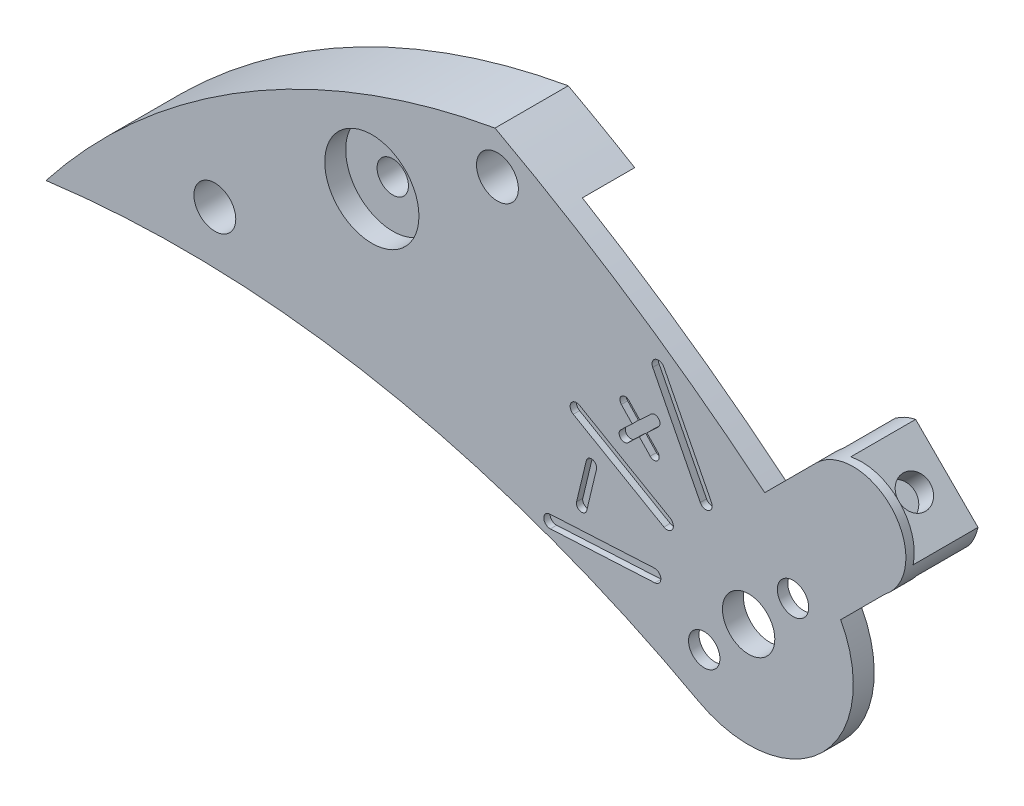
SolidWorks part; units mm, degrees
ref_plane "Alzado" through (0, 0, 0) normal (0, 0, 1) x (1, 0, 0)
ref_plane "Planta" through (0, 0, 0) normal (0, 1, 0) x (1, 0, 0)
ref_plane "Vista lateral" through (0, 0, 0) normal (1, 0, 0) x (0, 0, -1)
sketch "Croquis1" plane through (0, 0, 0) normal (0, 0, 1) x (1, 0, 0)
  line L0 (6.2596, 12.25) -> (5.199, 11.1893)
  line L1 (3.3861, 12.9119) -> (4.6235, 14.1494)
  line L2 (3, 10) -> (-3.9459, 10) construction
  line L4 (5.199, 11.1893) -> (8.6367, 11.1893) construction
  arc A0 (-3.0581, 17.2307) -> (-13.7828, 10.7835) centre (0, 0) ccw
  arc A1 (-3.5, 10) -> (-13.7828, 10.7835) centre (-10.5, -14) ccw
  arc A2 (1.7995, 7.8071) -> (5.199, 11.1893) centre (3, 10) ccw
  arc A3 (6.2596, 12.25) -> (4.6235, 14.1494) centre (5.5, 13.25) ccw
  arc A4 (3.3861, 12.9119) -> (-3.0581, 17.2307) centre (-22, -18) ccw
  arc A5 (-3.5, 10) -> (1.7995, 7.8071) centre (-10.9118, -15.4118) cw
  circle A7 centre (3, 10) radius 0.625
  circle A9 centre (-3, 16.25) radius 0.5
  circle A10 centre (-9.75, 12.25) radius 0.5
  dimension "D2" = 25
  dimension "D5" = 17.5
  dimension "D6" = 40
  dimension "D9" = 2.5
  dimension "D12" = 1.25
  dimension "D19" = 2.5
  dimension "D13" = 1.75
  dimension "D20" = 1
  dimension "D21" = 1
  dimension "D1" = 1.5
  dimension "D3" = 10.5
  dimension "D4" = 14
  dimension "D7" = 22
  dimension "D8" = 18
  dimension "D10" = 10
  dimension "D11" = 3
  dimension "D14" = 45
  dimension "D15" = 3
  dimension "D16" = 5.5
  dimension "D17" = 13.25
  dimension "D18" = 16.25
  dimension "D22" = 9.75
  dimension "D23" = 12.25
extrude "Saliente-Extruir1" add sketch "Croquis1" along normal blind 1.75
sketch "Croquis2" plane through (0, 0, 0) normal (0, 0, -1) x (-1, 0, 0)
  circle A0 centre (-3, 10) radius 7.75
  dimension "D1" = 15.5
extrude "Cortar-Extruir1" cut sketch "Croquis2" against normal blind 1.25
sketch "Croquis3" plane through (0, 0, 1.25) normal (0, 0, -1) x (-1, 0, 0)
  line L0 (-5.2726, 12.3236) -> (-4.5655, 13.0307)
  line L1 (-4.5655, 13.0307) -> (-4.919, 13.3843)
  line L2 (-4.919, 13.3843) -> (-5.6262, 12.6771)
  line L3 (-5.6262, 12.6771) -> (-5.2726, 12.3236)
  line L4 (-3.3861, 12.9119) -> (-4.6235, 14.1494) construction
  line L6 (-6.2596, 12.25) -> (-5.199, 11.1893) construction
  line L7 (-6.5086, 12.5018) -> (-4.7518, 14.2586)
  line L8 (-6.7284, 12.9891) -> (-5.2391, 14.4784)
  circle A0 centre (-3, 10) radius 0.625 construction
  arc A1 (-4.6235, 14.1494) -> (-6.2596, 12.25) centre (-5.5, 13.25) ccw construction
  arc A2 (-4.7518, 14.2586) -> (-5.2391, 14.4784) centre (-5.5, 13.25) ccw
  arc A3 (-6.7284, 12.9891) -> (-6.5086, 12.5018) centre (-5.5, 13.25) ccw
  dimension "D1" = 3.25
  dimension "D2" = 0.5
  dimension "D3" = 1
  dimension "D4" = 0.75
  dimension "D5" = 0.5
  dimension "D6" = 0.5
extrude "Saliente-Extruir2" add sketch "Croquis3" along normal blind 1.25
sketch "Croquis4" plane through (0, 0, 1.25) normal (0, 0, -1) x (-1, 0, 0)
  line L0 (-5.2391, 14.4784) -> (-6.7284, 12.9891) construction
  line L1 (-5.2391, 14.4784) -> (-6.7284, 12.9891)
  arc A0 (-5.2391, 14.4784) -> (-6.7284, 12.9891) centre (-5.5, 13.25) ccw construction
  arc A1 (-5.2391, 14.4784) -> (-6.7284, 12.9891) centre (-5.5, 13.25) ccw
extrude "Cortar-Extruir2" cut sketch "Croquis4" against normal blind 0.3
sketch "Croquis5" plane through (0, 0, 1.25) normal (0, 0, -1) x (-1, 0, 0)
  line L0 (-4.0607, 11.0607) -> (-1.9393, 8.9393) construction
  line L1 (-5.2726, 12.3236) -> (-4.5655, 13.0307) construction
  circle A0 centre (-4.0607, 11.0607) radius 0.75
  circle A1 centre (-1.9393, 8.9393) radius 0.75
  point P6 (-3, 10)
  point P7 (-3, 10)
  dimension "D2" = 1.5
  dimension "D3" = 1.5
  dimension "D1" = 3
extrude "Cortar-Extruir3" cut sketch "Croquis5" against normal blind 0.25
sketch "Croquis6" plane through (9.1517, 9.1517, 0) normal (0.7071, 0.7071, 0) x (0, 0, -1)
  line L0 (0, 5.9858) -> (-1.25, 5.9858) construction
  line L1 (0, 5.9858) -> (0, 4.9858) construction
  circle A0 centre (-0.625, 5.4858) radius 0.25 construction
  point P4 (-0.625, 5.9858)
  point P7 (0, 5.4858)
  dimension "D1" = 0.5
sketch "Croquis7" plane through (0, 0, 1.75) normal (0, 0, 1) x (1, 0, 0)
  circle A0 centre (-6, 14.5) radius 1.125
  dimension "D1" = 2.25
  dimension "D2" = 6
  dimension "D3" = 14.5
extrude "Cortar-Extruir4" cut sketch "Croquis7" against normal blind 0.5
ref_plane "Plano1" through (0, 0, 0.625) normal (0, 0, -1) x (-1, 0, 0)
sketch "Croquis8" plane through (0, 0, 1.75) normal (0, 0, 1) x (1, 0, 0)
  line L0 (0.8435, 14.2323) -> (1.9785, 12.0048) construction
  line L1 (0.9772, 14.3004) -> (2.1122, 12.0729)
  line L2 (0.7099, 14.1642) -> (1.8449, 11.9367)
  line L3 (0.7531, 9.8822) -> (-1.7435, 9.7514) construction
  line L4 (0.7609, 9.7324) -> (-1.7356, 9.6016)
  line L5 (0.7452, 10.032) -> (-1.7513, 9.9012)
  line L6 (1.9785, 12.0048) -> (3, 10) construction
  line L7 (0.7531, 9.8822) -> (3, 10) construction
  line L8 (3, 10) -> (-1.7983, 10) construction
  line L9 (3, 10) -> (-2.6707, 13.274) construction
  line L10 (-1.1136, 12.375) -> (1.0514, 11.125) construction
  line L11 (-1.0386, 12.5049) -> (1.1264, 11.2549)
  line L12 (-1.1886, 12.2451) -> (0.9764, 10.9951)
  line L13 (-0.7552, 11.4158) -> (-0.9887, 10.4434) construction
  line L14 (-0.6337, 11.3866) -> (-0.8671, 10.4142)
  line L15 (-0.8768, 11.4449) -> (-1.1102, 10.4726)
  line L16 (0.0322, 12.401) -> (0.7576, 13.0894) construction
  line L17 (-0.0538, 12.4917) -> (0.2182, 12.7498)
  line L18 (0.1183, 12.3104) -> (0.3903, 12.5685)
  line L19 (0.0507, 13.1079) -> (0.7391, 12.3825) construction
  line L20 (0.1414, 13.1939) -> (0.3995, 12.9219)
  line L21 (-0.0399, 13.0218) -> (0.2182, 12.7498)
  line L22 (3, 10) -> (-1.9711, 11.1935) construction
  line L23 (3, 10) -> (-0.4688, 13.6553) construction
  line L24 (0.3995, 12.9219) -> (0.6715, 13.1801)
  line L25 (0.5716, 12.7406) -> (0.8297, 12.4686)
  line L26 (0.3903, 12.5685) -> (0.6484, 12.2965)
  line L27 (0.5716, 12.7406) -> (0.8436, 12.9987)
  arc A0 (0.9772, 14.3004) -> (0.7099, 14.1642) centre (0.8435, 14.2323) ccw
  arc A1 (1.8449, 11.9367) -> (2.1122, 12.0729) centre (1.9785, 12.0048) ccw
  arc A2 (0.7609, 9.7324) -> (0.7452, 10.032) centre (0.7531, 9.8822) ccw
  arc A3 (-1.7513, 9.9012) -> (-1.7356, 9.6016) centre (-1.7435, 9.7514) ccw
  arc A4 (-1.0386, 12.5049) -> (-1.1886, 12.2451) centre (-1.1136, 12.375) ccw
  arc A5 (0.9764, 10.9951) -> (1.1264, 11.2549) centre (1.0514, 11.125) ccw
  arc A6 (-0.6337, 11.3866) -> (-0.8768, 11.4449) centre (-0.7552, 11.4158) ccw
  arc A7 (-1.1102, 10.4726) -> (-0.8671, 10.4142) centre (-0.9887, 10.4434) ccw
  arc A8 (-0.0538, 12.4917) -> (0.1183, 12.3104) centre (0.0322, 12.401) ccw
  arc A9 (0.8436, 12.9987) -> (0.6715, 13.1801) centre (0.7576, 13.0894) ccw
  arc A10 (0.1414, 13.1939) -> (-0.0399, 13.0218) centre (0.0507, 13.1079) ccw
  arc A11 (0.6484, 12.2965) -> (0.8297, 12.4686) centre (0.7391, 12.3825) ccw
  point P2 (1.411, 13.1185)
  point P9 (-0.4952, 9.8168)
  point P22 (-0.0311, 11.75)
  point P29 (-0.872, 10.9296)
  point P36 (0.3949, 12.7452)
  point P43 (0.3949, 12.7452)
  dimension "D1" = 30
  dimension "D2" = 2.25
  dimension "D3" = 2.25
  dimension "D4" = 33
  dimension "D5" = 33
  dimension "D6" = 2.25
  dimension "D7" = 2.5
  dimension "D8" = 2.5
  dimension "D9" = 2.5
  dimension "D10" = 0.3
  dimension "D11" = 0.3
  dimension "D12" = 0.3
  dimension "D13" = 16.5
  dimension "D14" = 16.5
  dimension "D15" = 0.25
  dimension "D16" = 0.25
  dimension "D17" = 1
  dimension "D18" = 1
  dimension "D19" = 0.25
  dimension "D20" = 1
extrude "Cortar-Extruir5" cut sketch "Croquis8" against normal blind 0.15
hole_wizard "M1x0.25 Tapped Hole1" positions "Croquis10" profile "Croquis9" tap size "M1x0.25" standard "KS" end condition through all
sketch "Croquis10" plane through (0, 0, 1.5) normal (0, 0, -1) x (-1, 0, 0)
  circle A1 centre (-4.0607, 11.0607) radius 0.75 construction
  circle A2 centre (-1.9393, 8.9393) radius 0.75 construction
  point P0 (-1.9393, 8.9393)
  point P1 (-4.0607, 11.0607)
sketch "Croquis9" plane through (1.9393, 8.9393, 1.5) normal (1, 0, 0) x (0, 1, 0)
  line L0 (0, 0) -> (0, 0.25)
  line L1 (0, 0.25) -> (0.375, 0.25)
  line L2 (0.375, 0.25) -> (0.375, 0)
  line L5 (0.375, 0) -> (0, 0)
  line L11 (0, -6.35) -> (0, 107.95) construction
  dimension "Diámetro de perforador para roscar hasta el siguiente" = 0.75
  dimension "Profundidad de perforador para roscar hasta el siguiente" = 0.25
cosmetic thread "Rosca de taladro1" parameters "D2"=1
cosmetic thread "Rosca de taladro2" parameters "D2"=1
hole_wizard "M1x0.25 Tapped Hole2" positions "Croquis12" profile "Croquis11" tap size "M1x0.25" standard "KS" end condition through all
sketch "Croquis12" plane through (0, 0, 1.25) normal (0, 0, 1) x (1, 0, 0)
  circle A0 centre (-6, 14.5) radius 1.125 construction
  point P0 (-6, 14.5)
sketch "Croquis11" plane through (-6, 14.5, 1.25) normal (1, 0, 0) x (0, -1, 0)
  line L0 (0, 0) -> (0, 1.25)
  line L1 (0, 1.25) -> (0.375, 1.25)
  line L2 (0.375, 1.25) -> (0.375, 0)
  line L5 (0.375, 0) -> (0, 0)
  line L11 (0, -6.35) -> (0, 107.95) construction
  dimension "Diámetro de perforador para roscar hasta el siguiente" = 0.75
  dimension "Profundidad de perforador para roscar hasta el siguiente" = 1.25
cosmetic thread "Rosca de taladro3" parameters "D2"=1
hole_wizard "M1x0.25 Tapped Hole3" positions "Croquis14" profile "Croquis13" tap size "M1x0.25" standard "KS" end condition up to next
sketch "Croquis14" plane through (9.8588, 9.8588, 0) normal (0.7071, 0.7071, 0) x (-0.7071, 0.7071, 0)
  line L0 (6.5332, 0) -> (4.427, 0) construction
  line L1 (4.427, 0) -> (4.427, 1.55) construction
  point P0 (5.4801, 0.775)
  point P5 (5.4801, 0)
  point P9 (4.427, 0.775)
cosmetic thread "Rosca de taladro4" parameters "D2"=1
sketch "Croquis13" plane through (5.9838, 13.7338, 0.775) normal (0, 0, 1) x (-0.7071, 0.7071, 0)
  line L0 (0, 0) -> (0, 0.5)
  line L1 (0, 0.5) -> (0.375, 0.5)
  line L2 (0.375, 0.5) -> (0.375, 0)
  line L5 (0.375, 0) -> (0, 0)
  line L11 (0, -6.35) -> (0, 107.95) construction
  dimension "Diámetro de perforador para roscar hasta el siguiente" = 0.75
  dimension "Profundidad de perforador para roscar hasta el siguiente" = 0.5
